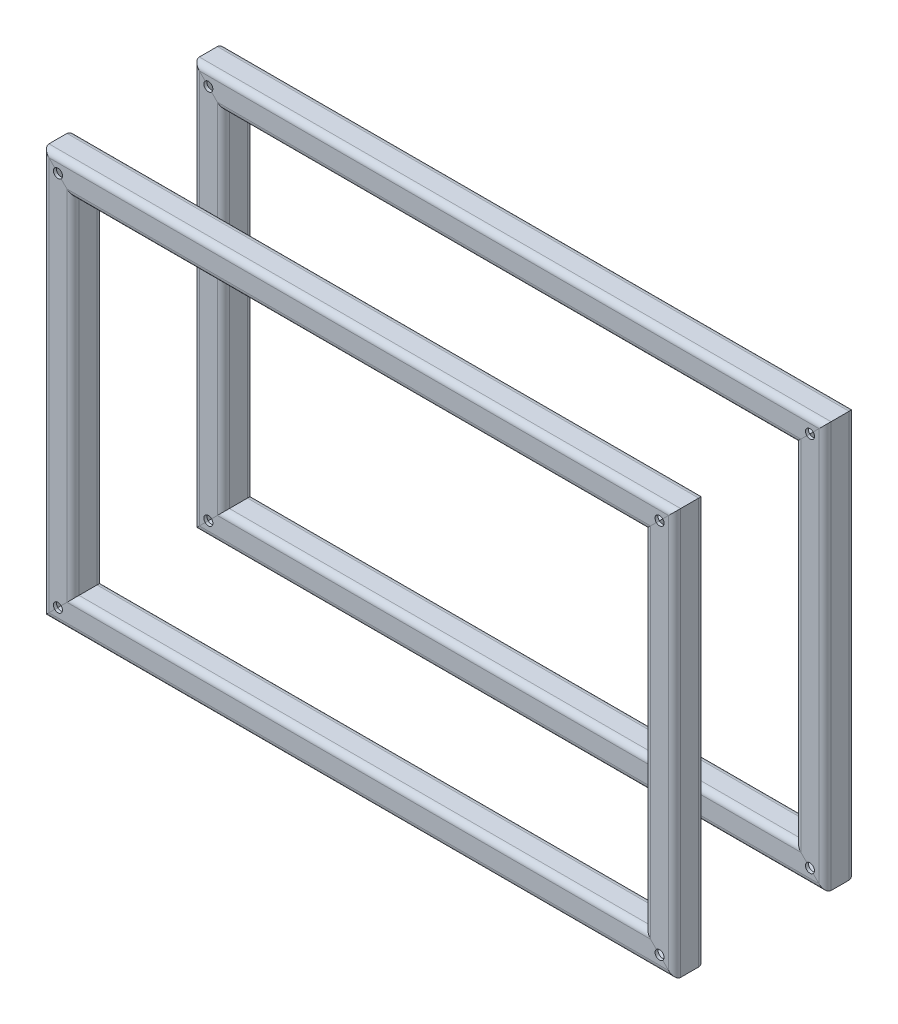
SolidWorks part; units mm, degrees
ref_plane "Ön Düzlem" through (0, 0, 0) normal (0, 0, 1) x (1, 0, 0)
ref_plane "Üst Düzlem" through (0, 0, 0) normal (0, 1, 0) x (1, 0, 0)
ref_plane "Sağ Düzlem" through (0, 0, 0) normal (1, 0, 0) x (0, 0, -1)
sketch3d "3B Çizim1"
  line L1 (-200, 125, 0) -> (200, 125, 0)
  line L2 (-200, 125, 0) -> (-200, -125, 0)
  line L3 (-200, -125, 0) -> (200, -125, 0)
  line L4 (200, 125, 0) -> (200, -125, 0)
  line L5 (-200, 125, 0) -> (200, -125, 0) construction
  line L6 (-200, -125, 0) -> (200, 125, 0) construction
  point P0 (0, 0, 0)
  dimension "D1" = 400
  dimension "D2" = 250
other "Kare tüp 20 X 20 X 2(1)"
ref_plane "Düzlem1" through (-200, 125, 0) normal (1, 0, 0) x (0, 0, -1)
sketch "Sketch1" plane through (-200, 125, 0) normal (1, 0, 0) x (0, 0, -1)
  line L0 (-6, -8) -> (6, -8)
  line L1 (-8, -6) -> (-8, 6)
  line L2 (6, 8) -> (-6, 8)
  line L3 (8, 6) -> (8, -6)
  line L4 (-6, -10) -> (6, -10)
  line L5 (-10, -6) -> (-10, 6)
  line L6 (6, 10) -> (-6, 10)
  line L7 (10, 6) -> (10, -6)
  arc A0 (10, 6) -> (6, 10) centre (6, 6) ccw
  arc A1 (6, -10) -> (10, -6) centre (6, -6) ccw
  arc A2 (-10, -6) -> (-6, -10) centre (-6, -6) ccw
  arc A3 (-6, 10) -> (-10, 6) centre (-6, 6) ccw
  arc A4 (-6, 8) -> (-8, 6) centre (-6, 6) ccw
  arc A5 (8, 6) -> (6, 8) centre (6, 6) ccw
  arc A6 (6, -8) -> (8, -6) centre (6, -6) ccw
  arc A7 (-8, -6) -> (-6, -8) centre (-6, -6) ccw
  point P0 (-10, 0)
  point P1 (10, 0)
  point P2 (0, 10)
  point P3 (0, -10)
  point P4 (0, 0)
  point P5 (-10, -10)
  point P6 (10, -10)
  point P7 (10, 10)
  point P8 (-10, 10)
  point P33 (0, 0)
  dimension "D1" = 4
  dimension "Thickness" = 2
  dimension "V_leg" = 20
ref_plane "Düzlem2" through (0, 0, 50) normal (0, 0, 1) x (1, 0, 0)
mirror "Aynalama2" about plane through (0, 0, 50) normal (0, 0, 1) of bodies 101 102 103 104
sketch "Çizim1" plane through (0, 0, 110) normal (0, 0, 1) x (1, 0, 0)
  line L0 (-206, 131) -> (-194, 119) construction
  line L1 (206, 131) -> (194, 119) construction
  line L2 (194, -119) -> (206, -131) construction
  line L3 (-194, -119) -> (-206, -131) construction
  circle A0 centre (-200, 125) radius 3
  circle A1 centre (200, 125) radius 3
  circle A2 centre (200, -125) radius 3
  circle A3 centre (-200, -125) radius 3
  dimension "D1" = 6
extrude "Kes-Ekstrüzyon1" cut sketch "Çizim1" against normal through all both and the other way through all
